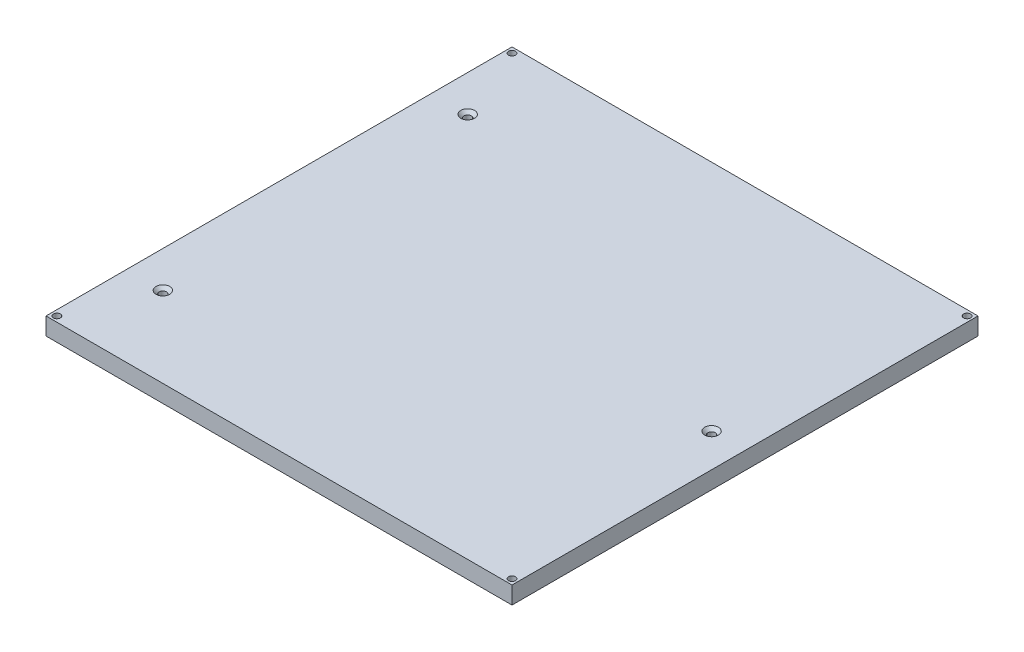
SolidWorks part; units mm, degrees
ref_plane "Plan de face" through (0, 0, 0) normal (0, 0, 1) x (1, 0, 0)
ref_plane "Plan de dessus" through (0, 0, 0) normal (0, 1, 0) x (1, 0, 0)
ref_plane "Plan de droite" through (0, 0, 0) normal (1, 0, 0) x (0, 0, -1)
sketch "Esquisse1" plane through (0, 0, 0) normal (0, 1, 0) x (1, 0, 0)
  line L0 (107, 107) -> (-107, -107) construction
  line L1 (-107, 107) -> (107, 107)
  line L2 (-107, 107) -> (-107, -107)
  line L3 (-107, -107) -> (107, -107)
  line L4 (107, 107) -> (107, -107)
  dimension "D1" = 214
  dimension "D2" = 214
extrude "Boss.-Extru.1" add sketch "Esquisse1" along normal blind 8
hole_wizard "Dégagement M31" positions "Esquisse3" profile "Esquisse4" hole size "M3" standard "Din" end condition through all
sketch "Esquisse3" plane through (0, 8, 0) normal (0, 1, 0) x (1, 0, 0)
  line L0 (-107, -107) -> (107, -107) construction
  line L1 (-107, 107) -> (-107, -107) construction
  line L2 (107, -107) -> (107, 107) construction
  line L3 (107, 107) -> (-107, 107) construction
  point P0 (-104.5, -104.5)
  point P2 (-104.5, 104.5)
  point P4 (104.5, 104.5)
  point P6 (104.5, -104.5)
  dimension "D1" = 2.5
  dimension "D2" = 2.5
  dimension "D3" = 2.5
  dimension "D4" = 2.5
  dimension "D5" = 2.5
  dimension "D6" = 2.5
  dimension "D7" = 2.5
  dimension "D8" = 2.5
sketch "Esquisse4" plane through (-104.5, 8, 104.5) normal (1, 0, 0) x (0, 0, 1)
  line L0 (0, 0) -> (0, 8)
  line L1 (0, 8) -> (1.6, 8)
  line L2 (1.6, 8) -> (1.6, 0)
  line L5 (1.6, 0) -> (0, 0)
  line L11 (0, -6.35) -> (0, 107.95) construction
  dimension "Diamètre du perçage jusqu'au prochain" = 3.2
  dimension "Profondeur du perçage jusqu'au prochain" = 8
hole_wizard "Fraisage pour vis à tête fraisée M31" positions "Esquisse6" profile "Esquisse5" countersink size "M3" standard "Din" end condition through all
sketch "Esquisse6" plane through (0, 8, 0) normal (0, 1, 0) x (1, 0, 0)
  circle A0 centre (91.6543, 0) radius 1.625 construction
  circle A3 centre (-90.3457, 70) radius 1.625 construction
  circle A4 centre (-90.3457, -70) radius 1.625 construction
  point P0 (-90.3457, 70)
  point P3 (-90.3457, -70)
  point P6 (91.6543, 0)
  point P9 (91.6543, 0)
sketch "Esquisse5" plane through (-90.3457, 8, -70) normal (1, 0, 0) x (0, 0, 1)
  line L0 (0, 0) -> (0, 8)
  line L1 (0, 8) -> (1.7, 8)
  line L2 (1.7, 8) -> (1.7, 1.45)
  line L3 (1.7, 1.45) -> (3.15, 0)
  line L5 (3.15, 0) -> (0, 0)
  line L6 (-1.7, 1.45) -> (-3.15, 0) construction
  line L11 (0, -6.35) -> (0, 107.95) construction
  dimension "Diamètre du perçage jusqu'au prochain" = 3.4
  dimension "Profondeur du perçage jusqu'au prochain" = 8
  dimension "Diamètre du fraisage entrant" = 6.3
  dimension "Angle du fraisage entrant" = 90
